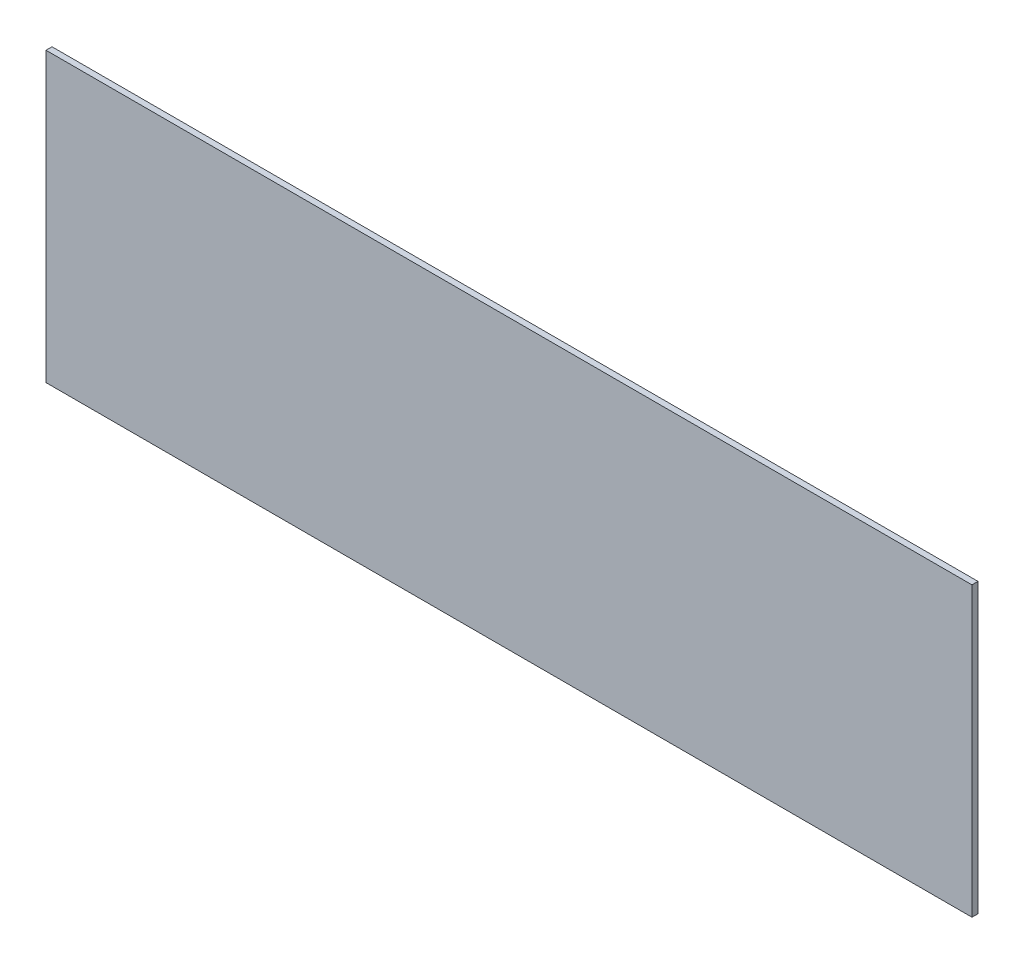
SolidWorks part; units mm, degrees
ref_plane "Front Plane" through (0, 0, 0) normal (0, 0, 1) x (1, 0, 0)
ref_plane "Top Plane" through (0, 0, 0) normal (0, 1, 0) x (1, 0, 0)
ref_plane "Right Plane" through (0, 0, 0) normal (1, 0, 0) x (0, 0, -1)
sketch "Sketch1" plane through (0, 0, 0) normal (0, 0, 1) x (1, 0, 0)
  line L0 (-230, -71.5) -> (-230, 68.5)
  line L1 (-230, 68.5) -> (-230, 71.5)
  line L2 (-230, 71.5) -> (230, 71.5)
  line L3 (230, 71.5) -> (230, -71.5)
  line L4 (230, -71.5) -> (-230, -71.5)
extrude "Boss-Extrude1" add sketch "Sketch1" along normal blind 3
